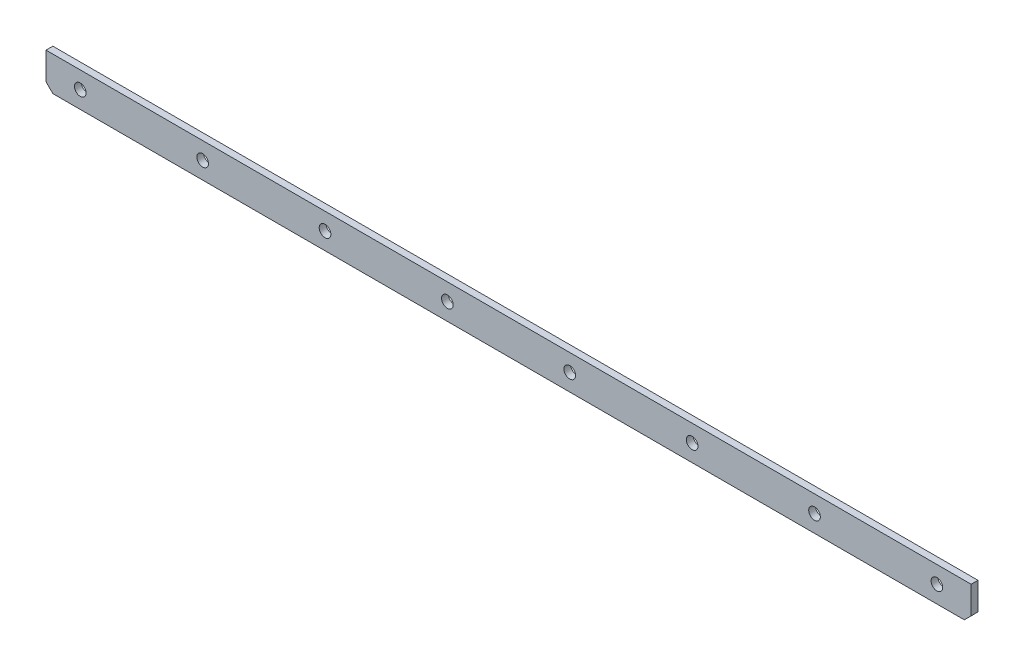
SolidWorks part; units mm, degrees
material "3.3315 (EN-AW 5005)"
ref_plane "Front Plane" through (0, 0, 0) normal (0, 0, 1) x (1, 0, 0)
ref_plane "Top Plane" through (0, 0, 0) normal (0, 1, 0) x (1, 0, 0)
ref_plane "Right Plane" through (0, 0, 0) normal (1, 0, 0) x (0, 0, -1)
sketch "Sketch1" plane through (0, 0, 0) normal (0, 0, 1) x (1, 0, 0)
  line L1 (135, -5) -> (-135, -5)
  line L2 (135, -5) -> (135, 5)
  line L3 (135, 5) -> (-135, 5)
  line L4 (-135, -5) -> (-135, 5)
  line L5 (135, -5) -> (-135, 5) construction
  line L6 (135, 5) -> (-135, -5) construction
  point P0 (0, 0)
  dimension "D1" = 270
  dimension "D2" = 10
extrude "Boss-Extrude1" add sketch "Sketch1" along normal blind 2
chamfer "Chamfer1" distance 2 angle 45 2 edges at (-135, -5, 1) (135, -5, 1)
hole_wizard "M3 Clearance Hole1" positions "Sketch2" profile "Sketch3" hole size "M3" standard "ISO" end condition through all
sketch "Sketch2" plane through (0, 0, 2) normal (0, 0, 1) x (1, 0, 0)
  line L0 (135, -3) -> (135, 5) construction
  line L1 (-133, -5) -> (133, -5) construction
  point P0 (125, 0)
  dimension "D1" = 10
  dimension "D2" = 5
sketch "Sketch3" plane through (125, 0, 2) normal (1, 0, 0) x (0, -1, 0)
  line L0 (0, 0) -> (0, 2)
  line L1 (0, 2) -> (1.7, 2)
  line L2 (1.7, 2) -> (1.7, 0)
  line L5 (1.7, 0) -> (0, 0)
  line L11 (0, -6.35) -> (0, 107.95) construction
  dimension "Thru Hole Dia." = 3.4
  dimension "Thru Hole Depth" = 2
pattern_linear "LPattern1" count 8 spacing 35.7143 along (-1, 0, 0) of "M3 Clearance Hole1"
